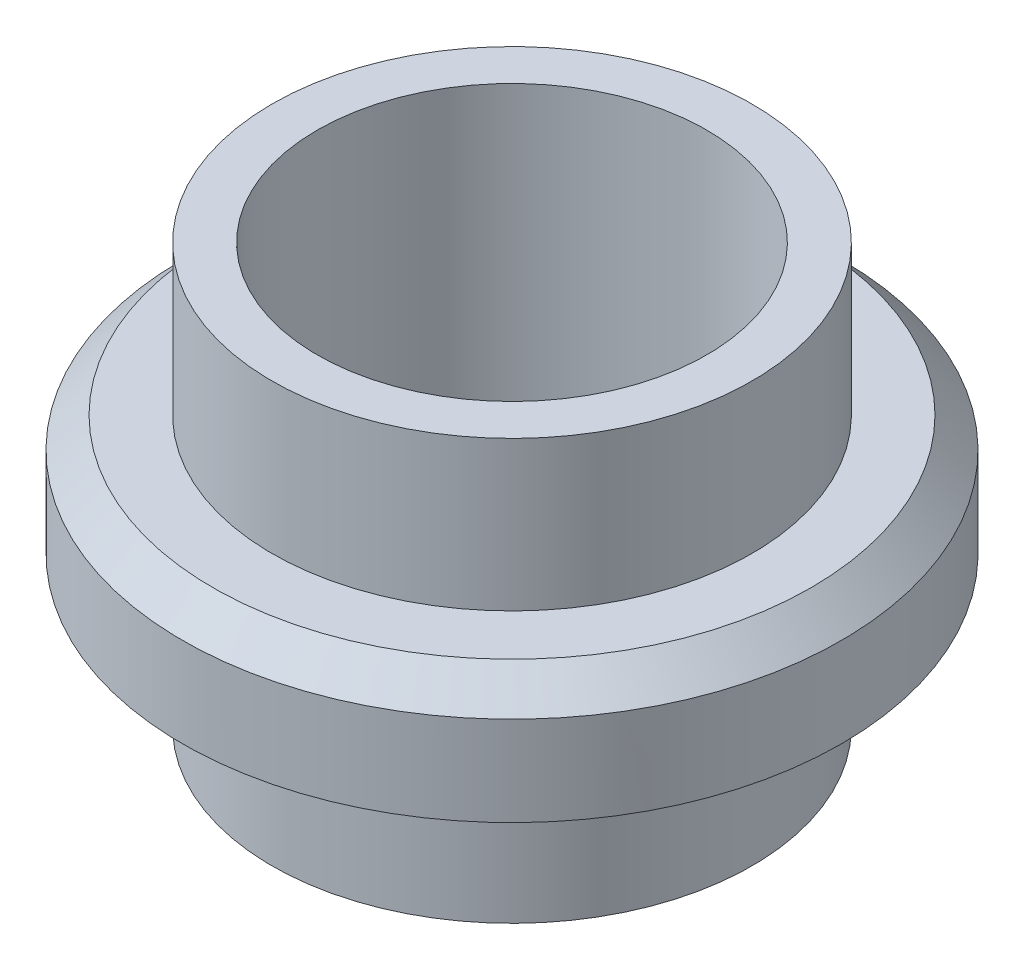
SolidWorks part; units mm, degrees
ref_plane "Front Plane" through (0, 0, 0) normal (0, 0, 1) x (1, 0, 0)
ref_plane "Top Plane" through (0, 0, 0) normal (0, 1, 0) x (1, 0, 0)
ref_plane "Right Plane" through (0, 0, 0) normal (1, 0, 0) x (0, 0, -1)
sketch "Sketch1" plane through (0, 0, 0) normal (0, 0, 1) x (1, 0, 0)
  line L0 (-1.886, 25.472) -> (-1.886, 8.2882)
  line L1 (-1.886, 25.472) -> (3.314, 25.472)
  line L2 (-1.886, 25.472) -> (-1.886, 8.2882)
  line L3 (-1.886, -22.828) -> (3.314, -22.828)
  line L4 (3.314, 25.472) -> (3.314, -22.828)
  line L5 (-12.186, 8.2882) -> (-1.886, 8.2882)
  line L6 (-12.186, 8.2882) -> (-12.186, 3.0882)
  line L7 (-8.686, 3.0882) -> (-1.886, 3.0882)
  line L10 (-12.186, 3.0882) -> (-12.186, -5.5118)
  line L11 (-12.186, -5.5118) -> (-8.686, -5.5118)
  line L12 (-8.686, 3.0882) -> (-8.686, -5.5118)
  line L13 (-1.886, 3.0882) -> (-1.886, -22.828)
  line L14 (25.714, 25.472) -> (25.714, -22.828)
  dimension "D1" = 5.2
  dimension "D2" = 48.3
  dimension "D3" = 10.3
  dimension "D4" = 5.2
  dimension "D5" = 3.5
  dimension "D6" = 8.6
  dimension "D7" = 22.4
revolve "Revolve2" add sketch "Sketch1" angle 360 about L14
chamfer "Chamfer1" distance 3.5 angle 45 1 edges at (-12.186, 8.2882, 0)
